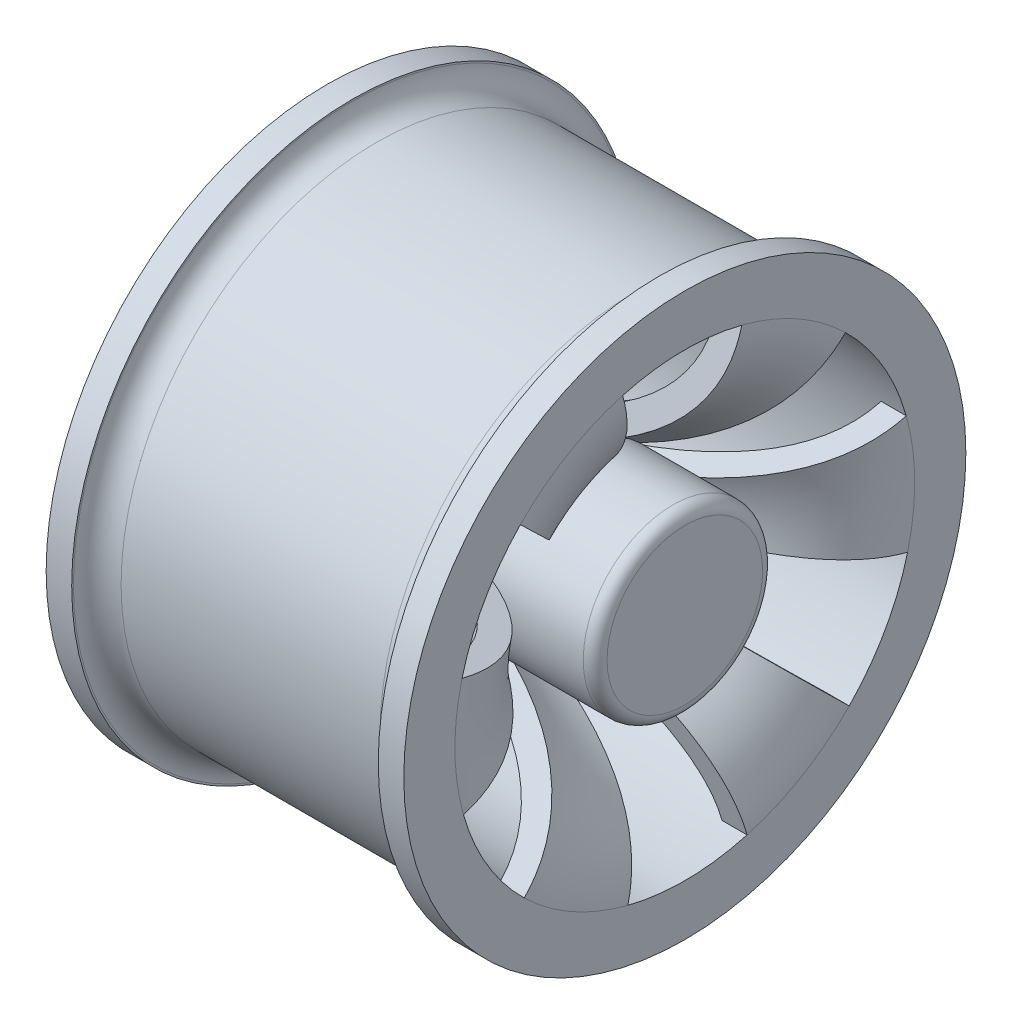
SolidWorks part; units mm, degrees
ref_plane "Front Plane" through (0, 0, 0) normal (0, 0, 1) x (1, 0, 0)
ref_plane "Top Plane" through (0, 0, 0) normal (0, 1, 0) x (1, 0, 0)
ref_plane "Right Plane" through (0, 0, 0) normal (1, 0, 0) x (0, 0, -1)
sketch "Sketch2" plane through (0, 0, 0) normal (0, 0, 1) x (1, 0, 0)
  line L0 (0, 0) -> (100.9154, 0) construction
  line L1 (0, 0) -> (0, 75.6089) construction
  line L2 (0, 75.6089) -> (0, 116.5961) construction
  line L3 (-38.1, 48.9858) -> (32.766, 48.9858)
  line L4 (38.1, 48.9858) -> (38.1, 59.8715)
  line L5 (38.1, 59.8715) -> (32.6571, 59.8715)
  line L7 (32.6571, 59.8715) -> (32.6571, 59.5086)
  line L8 (27.5771, 54.4286) -> (-27.5771, 54.4286)
  line L9 (-32.6571, 59.8715) -> (-32.6571, 59.5086)
  line L10 (-38.1, 59.8715) -> (-32.6571, 59.8715)
  line L11 (-38.1, 48.9858) -> (-38.1, 59.8715)
  line L12 (38.1, 41.7407) -> (38.1, 56.231) construction
  line L13 (0, 13.589) -> (0, 19.1081)
  arc A0 (32.6571, 59.5086) -> (27.5771, 54.4286) centre (27.5771, 59.5086) cw
  arc A1 (-32.6571, 59.5086) -> (-27.5771, 54.4286) centre (-27.5771, 59.5086) ccw
  spline S0 degree 3 poles (38.1, 48.9858) (38.1, 28.3876) (15.6824, 17.6076) (0, 13.589) knots 0 0 0 0 1 1 1 1
  spline S1 degree 1 poles (32.766, 48.9858) (-1.3241, 18.7561) knots 0 0 1 1 construction
  spline S2 degree 3 poles (32.766, 48.9858) (32.766, 48.4732) (32.7305, 47.4345) (32.5256, 45.4722) (32.0321, 43.1395) (31.0896, 40.514) (29.3887, 37.1947) (26.4603, 33.3453) (21.8332, 29.2167) (16.3781, 25.6516) (11.4284, 23.1882) (7.4089, 21.5301) (4.4096, 20.4423) (1.9659, 19.6659) (0.0587, 19.1196) (-0.859, 18.8752) (-1.3241, 18.7561) knots 0 0 0 0 0.03125 0.0625 0.125 0.1875 0.25 0.375 0.5 0.625 0.75 0.8125 0.875 0.9375 0.96875 1 1 1 1 only from (32.766, 48.9858) to (0, 19.1081)
  point P14 (32.6571, 54.4286)
  point P19 (0, 54.4286)
  point P20 (0, 48.9858)
  dimension "D5" = 5.08
  dimension "D9" = 5.334
  dimension "D1" = 38.1
  dimension "D2" = 10.8857
  dimension "D3" = 5.4429
  dimension "D4" = 5.4429
  dimension "D6" = 54.4286
  dimension "D7" = 13.589
  dimension "D8" = 27.178
revolve "Revolve6" add sketch "Sketch2" angle 360 about L0
sketch "Sketch3" plane through (-38.1, 0, 0) normal (-1, 0, 0) x (0, 0, 1)
  circle A0 centre (0, 0) radius 13.589 construction
  circle A1 centre (0, 0) radius 13.589
  circle A2 centre (0, 0) radius 19.1081 construction
  circle A3 centre (0, 0) radius 19.1081
extrude "Boss-Extrude1" add sketch "Sketch3" against normal blind 76.2 separate body
sketch "Sketch4" plane through (38.1, 0, 0) normal (1, 0, 0) x (0, 0, -1)
  circle A0 centre (0, 0) radius 19.1081 construction
  circle A1 centre (0, 0) radius 19.1081
extrude "Boss-Extrude2" add sketch "Sketch4" against normal blind 12.7
sketch "Sketch5" plane through (38.1, 0, 0) normal (1, 0, 0) x (0, 0, -1)
  line L1 (-5.1722, 18.3948) -> (-13.2595, 47.1571)
  line L2 (4.7357, 18.512) -> (12.1405, 47.4576)
  circle A0 centre (0, 0) radius 19.1081 construction
  circle A1 centre (0, 0) radius 19.1081
  circle A2 centre (0, 0) radius 48.9858 construction
  circle A3 centre (0, 0) radius 48.9858
  circle M5 centre (0, 0) radius 48.9858
  dimension "D1" = 25.4
extrude "Cut-Extrude1" cut sketch "Sketch5" against normal through all contours A1 L2 L1 M5
pattern_circular "CirPattern5" count 6 over 360 about axis through (0, 0, 0) along (1, 0, 0) of "Cut-Extrude1"
fillet "Fillet3" radius 2.54 1 edges at (38.1, 0, 19.1081)
